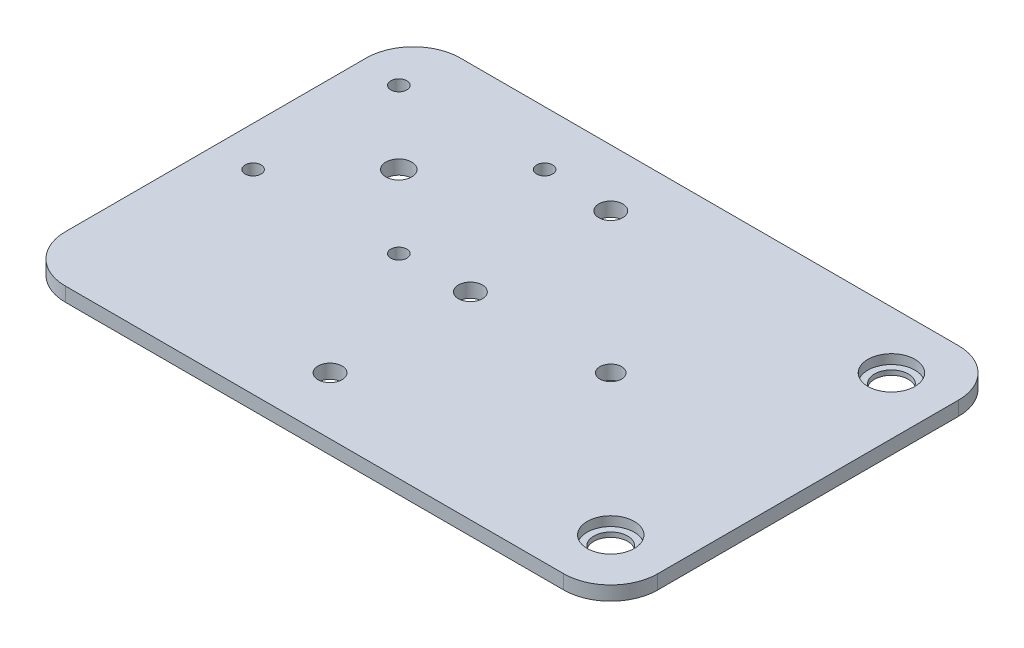
SolidWorks part; units mm, degrees
material "3003 Alloy"
ref_plane "Спереди" through (0, 0, 0) normal (0, 0, 1) x (1, 0, 0)
ref_plane "Сверху" through (0, 0, 0) normal (0, 1, 0) x (1, 0, 0)
ref_plane "Справа" through (0, 0, 0) normal (1, 0, 0) x (0, 0, -1)
ref_plane "Plane1" through (0, 6, 0) normal (0, 1, 0) x (1, 0, 0)
sketch "Sketch1" plane through (0, 6, 0) normal (0, 1, 0) x (1, 0, 0)
  line L0 (42, 42) -> (-42, 42)
  line L1 (-42, 42) -> (-42, -42) construction
  line L2 (-42, 42) -> (42, -42) construction
  line L3 (42, 42) -> (-42, -42) construction
  line L4 (-42, -42) -> (42, -42)
  line L5 (42, -42) -> (42, 42)
  line L7 (-42, 42) -> (-84, 42)
  line L8 (-42, 42) -> (-42, -42) construction
  line L9 (-42, -42) -> (-84, -42)
  line L10 (-84, 42) -> (-84, -42)
  point P0 (0, 0)
  dimension "D1" = 84
  dimension "D2" = 84
  dimension "D3" = 42
extrude "Boss-Extrude1" add sketch "Sketch1" against normal blind 3
hole_wizard "Ø4.6 (4.6) Diameter Hole1" positions "Sketch10" profile "Sketch9" hole size "Ø4.6" standard "ANSI Metric" end condition through all
sketch "Sketch10" plane through (0, 3, 0) normal (0, -1, 0) x (-1, 0, 0)
  point P2 (0, 0)
sketch "Sketch9" plane through (0, 3, 0) normal (1, 0, 0) x (0, 0, -1)
  line L0 (0, 0) -> (0, 3)
  line L1 (0, 3) -> (2.3, 3)
  line L2 (2.3, 3) -> (2.3, 0)
  line L5 (2.3, 0) -> (0, 0)
  line L11 (0, -6.35) -> (0, 107.95) construction
  dimension "Thru Hole Dia." = 4.6
  dimension "Thru Hole Depth" = 3
hole_wizard "CBORE for M6.5 SHSS1" positions "Sketch12" profile "Sketch11" counterbore size "M6.5" standard "ANSI Metric" end condition through all
sketch "Sketch12" plane through (0, 6, 0) normal (0, 1, 0) x (1, 0, 0)
  point P0 (29.85, 29.85)
  point P9 (29.85, -29.85)
  dimension "D1" = 29.85
  dimension "D2" = 29.85
  dimension "D3" = 29.85
sketch "Sketch11" plane through (29.85, 6, -29.85) normal (1, 0, 0) x (0, 0, 1)
  line L0 (0, 0) -> (0, 3)
  line L1 (0, 3) -> (3.6, 3)
  line L3 (3.6, 3) -> (3.6, 2)
  line L4 (3.6, 2) -> (5, 2)
  line L5 (5, 2) -> (5, 0)
  line L7 (5, 0) -> (0, 0)
  line L11 (0, -6.35) -> (0, 107.95) construction
  dimension "Thru Hole Dia." = 7.2
  dimension "Thru Hole Depth" = 3
  dimension "C'Bore Dia." = 10
  dimension "C'Bore Depth" = 2
hole_wizard "M10x1.0 Tapped Hole1" positions "Sketch14" profile "Sketch13" tap size "M10x1.0" standard "ANSI Metric" end condition through all
sketch "Sketch14" plane through (0, 6, 0) normal (0, 1, 0) x (1, 0, 0)
  point P0 (-29.85, -29.85)
  point P1 (-29.85, 29.85)
  point P17 (-29.85, 0)
  dimension "D1" = 29.85
sketch "Sketch13" plane through (-29.85, 6, 29.85) normal (1, 0, 0) x (0, 0, 1)
  line L0 (0, 0) -> (0, 3)
  line L1 (0, 3) -> (2.55, 3)
  line L2 (2.55, 3) -> (2.55, 0)
  line L5 (2.55, 0) -> (0, 0)
  line L11 (0, -6.35) -> (0, 107.95) construction
  dimension "Thru Tap Drill Dia." = 5.1
  dimension "Thru Tap Drill Depth" = 3
sketch "Sketch18" plane through (0, 6, 0) normal (0, 1, 0) x (1, 0, 0)
  line L1 (-29.85, 29.85) -> (-29.85, 0) construction
  line L2 (-84, 42) -> (-84, -42) construction
  line L6 (-81, 35.925) -> (-39, 35.925) construction
  line L7 (-81, 35.925) -> (-81, -6.075) construction
  line L8 (-81, -6.075) -> (-39, -6.075) construction
  line L9 (-39, 35.925) -> (-39, -6.075) construction
  line L10 (-81, 35.925) -> (-39, -6.075) construction
  line L11 (-81, -6.075) -> (-39, 35.925) construction
  circle A0 centre (-29.85, 29.85) radius 2.55 construction
  circle A1 centre (-29.85, 0) radius 2.55 construction
  point P0 (-60, 14.925)
  point P1 (-75.5, 30.425)
  point P2 (-44.5, 30.425)
  point P3 (-44.5, -0.575)
  point P4 (-75.5, -0.575)
  point P7 (-60, 14.925)
  point P8 (-29.85, 29.85)
  point P9 (-29.85, 14.925)
  point P12 (0, 0)
  point P13 (0, 0)
  point P18 (0, 0)
  point P19 (0, 0)
  point P21 (0, 0)
  point P25 (0, 0)
  dimension "D1" = 31
  dimension "D2" = 42
  dimension "D3" = 3
  dimension "D4" = 15.5
hole_wizard "Ø3.0mm Dowel Hole1" positions "Sketch20" profile "Sketch22" hole size "Ø3.0" standard "ANSI Metric" end condition through all
sketch "Sketch20" plane through (0, 6, 0) normal (0, 1, 0) x (1, 0, 0)
  point P0 (-75.5, 30.425)
  point P3 (-44.5, 30.425)
  point P6 (-44.5, -0.575)
  point P9 (-75.5, -0.575)
sketch "Sketch22" plane through (-75.5, 6, -30.425) normal (1, 0, 0) x (0, 0, 1)
  line L0 (0, 0) -> (0, 3)
  line L1 (0, 3) -> (1.7, 3)
  line L2 (1.7, 3) -> (1.7, 0)
  line L5 (1.7, 0) -> (0, 0)
  line L11 (0, -6.35) -> (0, 107.95) construction
  dimension "Thru Hole Dia." = 3.4
  dimension "Thru Hole Depth" = 3
hole_wizard "Ø5.0mm Dowel Hole1" positions "Sketch23" profile "Sketch24" hole size "Ø5.0" standard "ANSI Metric" end condition through all
sketch "Sketch23" plane through (0, 6, 0) normal (0, 1, 0) x (1, 0, 0)
  line L0 (-81, 35.925) -> (-39, -6.075) construction
  point P0 (-60, 14.925)
sketch "Sketch24" plane through (-60, 6, -14.925) normal (1, 0, 0) x (0, 0, 1)
  line L0 (0, 0) -> (0, 3)
  line L1 (0, 3) -> (2.75, 3)
  line L2 (2.75, 3) -> (2.75, 0)
  line L5 (2.75, 0) -> (0, 0)
  line L11 (0, -6.35) -> (0, 107.95) construction
  dimension "Thru Hole Dia." = 5.5
  dimension "Thru Hole Depth" = 3
fillet "Fillet3" radius 10 4 edges at (42, 4.5, -42) (42, 4.5, 42) (-84, 4.5, 42) (-84, 4.5, -42)
sketch "Sketch25" plane through (0, 6, 0) normal (0, 1, 0) x (1, 0, 0)
  line L0 (42, 42) -> (-42, -42) construction
  line L1 (-42, 42) -> (42, -42) construction
  point P0 (0, 0)
equation "\"D4@Sketch18\"=\"D1@Sketch18\"/2"
equation "\"D3@Sketch12\"=\"D1@Sketch12\""
equation "\"D1@Sketch12\"=\"D2@Sketch12\""
equation "\"Wheel spacing\"= 59.7mm"
equation "\"D2@Sketch12\"=\"Wheel spacing\"/2"
equation "\"D1@Sketch14\"=\"Wheel spacing\"/2"
